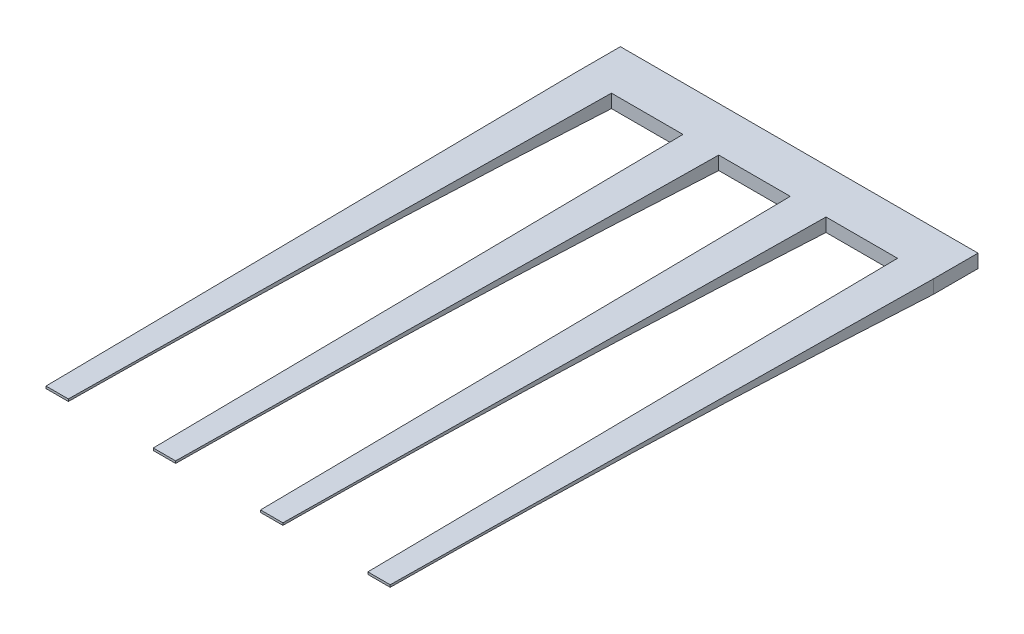
SolidWorks part; units mm, degrees
ref_plane "Front Plane" through (0, 0, 0) normal (0, 0, 1) x (1, 0, 0)
ref_plane "Top Plane" through (0, 0, 0) normal (0, 1, 0) x (1, 0, 0)
ref_plane "Right Plane" through (0, 0, 0) normal (1, 0, 0) x (0, 0, -1)
sketch "Sketch1" plane through (0, 0, 0) normal (0, 0, 1) x (1, 0, 0)
  line L1 (0, 0) -> (1600, 0)
  line L2 (0, 0) -> (0, -60)
  line L3 (0, -60) -> (1600, -60)
  line L4 (1600, 0) -> (1600, -60)
  dimension "D1" = 60
  dimension "D2" = 1600
extrude "Boss-Extrude1" add sketch "Sketch1" along normal blind 200
ref_plane "Plane1" through (0, 0, 1400) normal (0, 0, 1) x (1, 0, 0)
ref_plane "Plane2" through (0, 0, 2600) normal (0, 0, 1) x (1, 0, 0)
sketch "Sketch2" plane through (0, 0, 200) normal (0, 0, 1) x (1, 0, 0)
  line L1 (0, 0) -> (160, 0)
  line L2 (0, 0) -> (0, -60)
  line L3 (0, -60) -> (160, -60)
  line L4 (160, 0) -> (160, -60)
  dimension "D1" = 60
  dimension "D2" = 160
sketch "Sketch3" plane through (0, 0, 1400) normal (0, 0, 1) x (1, 0, 0)
  line L0 (0, 0) -> (160, 0) construction
  line L1 (15, 0) -> (145, 0)
  line L2 (15, 0) -> (15, -20)
  line L3 (15, -20) -> (145, -20)
  line L4 (145, 0) -> (145, -20)
  line L5 (0, 0) -> (0, -60) construction
  dimension "D1" = 20
  dimension "D2" = 130
  dimension "D3" = 15
sketch "Sketch4" plane through (0, 0, 2600) normal (0, 0, 1) x (1, 0, 0)
  line L0 (0, 0) -> (160, 0) construction
  line L1 (30, 0) -> (130, 0)
  line L2 (30, 0) -> (30, -10)
  line L3 (30, -10) -> (130, -10)
  line L4 (130, 0) -> (130, -10)
  dimension "D1" = 10
  dimension "D2" = 100
  dimension "D3" = 30
loft "Loft1" add profiles "Sketch2", "Sketch3", "Sketch4"
pattern_linear "LPattern1" count 4 spacing 480 along (1, 0, 0) of "Loft1"
